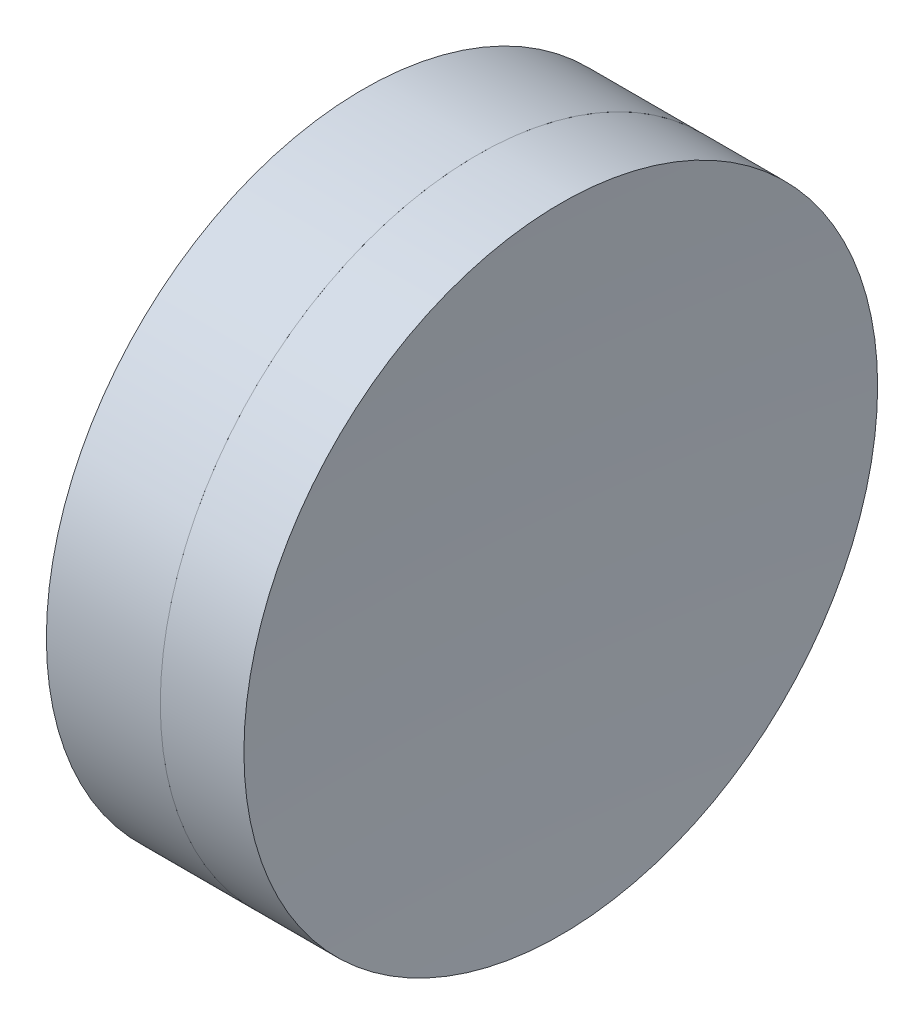
SolidWorks part; units mm, degrees
ref_plane "前视基准面" through (0, 0, 0) normal (0, 0, 1) x (1, 0, 0)
ref_plane "上视基准面" through (0, 0, 0) normal (0, 1, 0) x (1, 0, 0)
ref_plane "右视基准面" through (0, 0, 0) normal (1, 0, 0) x (0, 0, -1)
sketch "草图1" plane through (0, 0, 0) normal (0, 1, 0) x (1, 0, 0)
  line L0 (-0.8161, 0) -> (252.2923, 0) construction
  line L1 (217.1878, 12.5) -> (221.682, 12.5)
  line L4 (217.1878, -12.5) -> (221.682, -12.5)
  arc A0 (217.1878, -12.5) -> (217.1878, 12.5) centre (125.7381, 0) ccw
  arc A1 (221.682, 12.5) -> (221.682, -12.5) centre (289.4081, 0) ccw
  point P6 (218.0381, 0)
  point P8 (220.5381, 0)
  dimension "D3" = 12.5
  dimension "D4" = 2.5
  dimension "D1" = 92.3
  dimension "D5" = 68.87
  dimension "D2" = 12.5
revolve "旋转1" add sketch "草图1" angle 360 about L0
sketch "草图2" plane through (0, 0, 0) normal (0, 1, 0) x (1, 0, 0)
  line L2 (217.1878, 0) -> (249.4445, 0) construction
  line L3 (217.1878, -12.5) -> (217.1878, 12.5) construction
  line L6 (221.682, 12.5) -> (224.9812, 12.5)
  line L7 (221.682, -12.5) -> (224.9812, -12.5)
  arc A2 (221.682, 12.5) -> (221.682, -12.5) centre (289.4081, 0) ccw construction
  arc A3 (221.682, 12.5) -> (221.682, -12.5) centre (289.4081, 0) ccw
  arc A4 (224.9812, 12.5) -> (224.9812, -12.5) centre (428.7481, 0) ccw
  point P8 (220.5381, 0)
  point P9 (224.5981, 0)
  dimension "D1" = 4.06
  dimension "D2" = 204.15
revolve "旋转3" add sketch "草图2" angle 360 about L2
